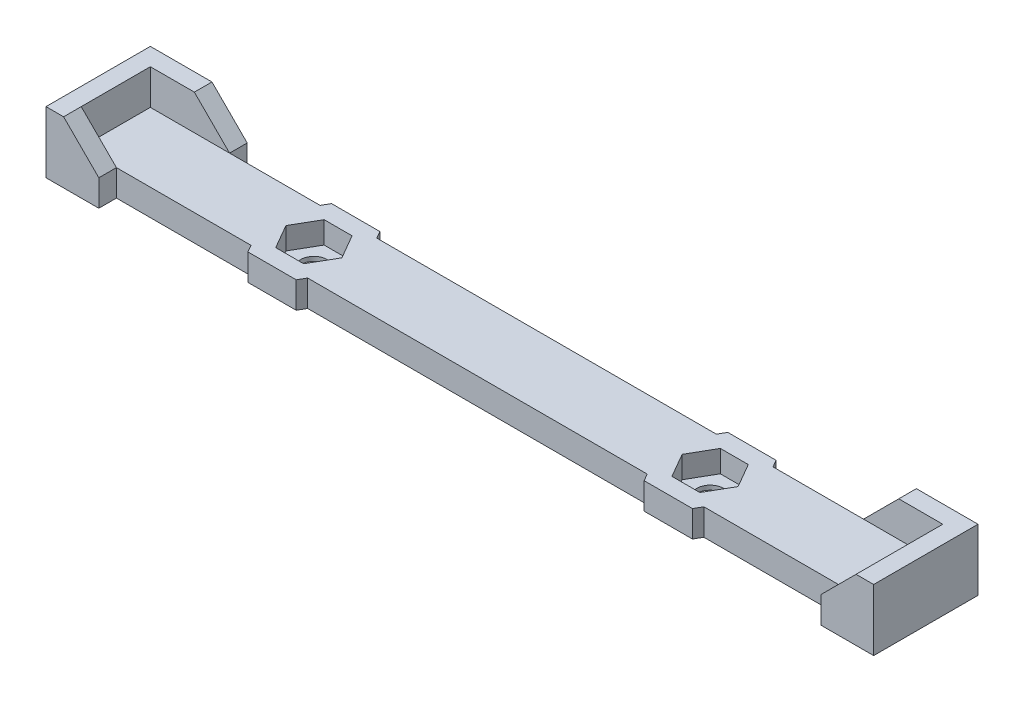
SolidWorks part; units mm, degrees
ref_plane "前视基准面" through (0, 0, 0) normal (0, 0, 1) x (1, 0, 0)
ref_plane "上视基准面" through (0, 0, 0) normal (0, 1, 0) x (1, 0, 0)
ref_plane "右视基准面" through (0, 0, 0) normal (1, 0, 0) x (0, 0, -1)
sketch "草图1" plane through (0, 0, 0) normal (0, 1, 0) x (1, 0, 0)
  line L0 (0, 0) -> (90, 0)
  line L1 (0, 0) -> (0, -7.85)
  line L2 (90, 0) -> (90, -7.85)
  line L3 (0, -7.85) -> (90, -7.85)
  point P7 (91.2972, -17.025)
  dimension "D1" = 90
  dimension "D2" = 7.85
extrude "凸台-拉伸1" add sketch "草图1" along normal blind 2
sketch "草图2" plane through (90, 0, 0) normal (1, 0, 0) x (0, 0, -1)
  line L0 (-7.85, 0) -> (-7.85, 6)
  line L1 (-7.85, 0) -> (0, 0)
  line L2 (-7.85, 6) -> (0, 6)
  line L3 (0, 0) -> (0, 6)
  dimension "D1" = 7.85
  dimension "D2" = 6
extrude "凸台-拉伸2" add sketch "草图2" along normal blind 2
sketch "草图3" plane through (0, 0, 0) normal (-1, 0, 0) x (0, 0, 1)
  line L0 (0, 0) -> (0, 6)
  line L1 (0, 0) -> (7.85, 0)
  line L2 (0, 6) -> (7.85, 6)
  line L3 (7.85, 0) -> (7.85, 6)
  dimension "D1" = 7.85
extrude "凸台-拉伸3" add sketch "草图3" along normal blind 2
sketch "草图4" plane through (0, 0, 0) normal (0, 0, -1) x (-1, 0, 0)
  line L0 (2, 0) -> (2, 6)
  line L1 (2, 6) -> (0, 6)
  line L2 (0, 6) -> (-5, 6)
  line L3 (-5, 6) -> (-9, 2)
  line L4 (-90, 2) -> (0, 2) construction
  line L5 (-9, 2) -> (-9, 0)
  line L6 (-92, 0) -> (2, 0) construction
  line L7 (-9, 0) -> (2, 0)
  line L8 (-92, 0) -> (-92, 6)
  line L9 (-92, 6) -> (-90, 6)
  line L10 (-90, 6) -> (-85, 6)
  line L11 (-85, 6) -> (-81, 2)
  line L12 (-81, 2) -> (-81, 0)
  line L13 (-81, 0) -> (-92, 0)
  dimension "D1" = 5
  dimension "D2" = 4
  dimension "D3" = 5
  dimension "D4" = 4
extrude "凸台-拉伸4" add sketch "草图4" along normal blind 2
sketch "草图5" plane through (0, 0, 7.85) normal (0, 0, 1) x (1, 0, 0)
  line L0 (92, 0) -> (92, 6)
  line L1 (92, 6) -> (90, 6)
  line L2 (90, 6) -> (86, 2)
  line L3 (90, 2) -> (81, 2) construction
  line L4 (86, 2) -> (86, 0)
  line L5 (-2, 0) -> (92, 0) construction
  line L6 (86, 0) -> (92, 0)
  line L7 (-2, 0) -> (-2, 6)
  line L8 (-2, 6) -> (0, 6)
  line L9 (0, 6) -> (4, 2)
  line L10 (9, 2) -> (0, 2) construction
  line L11 (4, 2) -> (4, 0)
  line L12 (4, 0) -> (-2, 0)
  dimension "D1" = 4
  dimension "D2" = 4
extrude "凸台-拉伸5" add sketch "草图5" along normal blind 2
sketch "草图10" plane through (0, 0, 0) normal (0, -1, 0) x (1, 0, 0)
  line L0 (-2, -2) -> (-2, 9.85)
  line L1 (-2, 9.85) -> (4, 9.85)
  line L2 (4, 9.85) -> (4, 7.85)
  line L3 (4, 7.85) -> (86, 7.85)
  line L4 (86, 7.85) -> (86, 9.85)
  line L5 (86, 9.85) -> (92, 9.85)
  line L6 (92, 9.85) -> (92, -2)
  line L7 (92, -2) -> (81, -2)
  line L8 (81, -2) -> (81, 0)
  line L9 (81, 0) -> (9, 0)
  line L10 (9, 0) -> (9, -2)
  line L11 (9, -2) -> (-2, -2)
extrude "凸台-拉伸8" add sketch "草图10" along normal blind 1
sketch "草图12" plane through (0, 2, 0) normal (0, 1, 0) x (1, 0, 0)
  line L4 (25.6754, -3.925) -> (24.0877, -1.175)
  line L5 (24.0877, -1.175) -> (20.9123, -1.175)
  line L6 (20.9123, -1.175) -> (19.3246, -3.925)
  line L7 (19.3246, -3.925) -> (20.9123, -6.675)
  line L8 (20.9123, -6.675) -> (24.0877, -6.675)
  line L9 (24.0877, -6.675) -> (25.6754, -3.925)
  line L11 (70.6754, -3.925) -> (69.0877, -1.175)
  line L12 (69.0877, -1.175) -> (65.9123, -1.175)
  line L13 (65.9123, -1.175) -> (64.3246, -3.925)
  line L14 (64.3246, -3.925) -> (65.9123, -6.675)
  line L15 (65.9123, -6.675) -> (69.0877, -6.675)
  line L16 (69.0877, -6.675) -> (70.6754, -3.925)
  circle A0 centre (22.5, -3.925) radius 2.75 construction
  circle A1 centre (67.5, -3.925) radius 2.75 construction
  dimension "D2" = 5.5
  dimension "D3" = 5.5
extrude "切除-拉伸1" cut sketch "草图12" against normal blind 2.5
sketch "草图13" plane through (0, 2, 0) normal (0, 1, 0) x (1, 0, 0)
  line L1 (27.9848, -3.925) -> (25.2424, 0.825)
  line L2 (25.2424, 0.825) -> (19.7576, 0.825)
  line L3 (19.7576, 0.825) -> (17.0152, -3.925)
  line L4 (17.0152, -3.925) -> (19.7576, -8.675)
  line L5 (19.7576, -8.675) -> (25.2424, -8.675)
  line L6 (24.0877, -6.675) -> (25.6754, -3.925)
  line L7 (25.6754, -3.925) -> (24.0877, -1.175)
  line L8 (24.0877, -1.175) -> (20.9123, -1.175)
  line L9 (20.9123, -1.175) -> (19.3246, -3.925)
  line L10 (19.3246, -3.925) -> (20.9123, -6.675)
  line L11 (20.9123, -6.675) -> (24.0877, -6.675)
  line L12 (24.0877, -6.675) -> (25.6754, -3.925)
  line L13 (25.6754, -3.925) -> (24.0877, -1.175)
  line L14 (24.0877, -1.175) -> (20.9123, -1.175)
  line L15 (20.9123, -1.175) -> (19.3246, -3.925)
  line L16 (19.3246, -3.925) -> (20.9123, -6.675)
  line L17 (20.9123, -6.675) -> (24.0877, -6.675)
  line L18 (69.0877, -6.675) -> (70.6754, -3.925)
  line L19 (70.6754, -3.925) -> (69.0877, -1.175)
  line L20 (69.0877, -1.175) -> (65.9123, -1.175)
  line L21 (65.9123, -1.175) -> (64.3246, -3.925)
  line L22 (64.3246, -3.925) -> (65.9123, -6.675)
  line L23 (65.9123, -6.675) -> (69.0877, -6.675)
  line L24 (69.0877, -6.675) -> (70.6754, -3.925)
  line L25 (70.6754, -3.925) -> (69.0877, -1.175)
  line L26 (69.0877, -1.175) -> (65.9123, -1.175)
  line L27 (65.9123, -1.175) -> (64.3246, -3.925)
  line L28 (64.3246, -3.925) -> (65.9123, -6.675)
  line L29 (65.9123, -6.675) -> (69.0877, -6.675)
  line L30 (25.2424, -8.675) -> (27.9848, -3.925)
  line L31 (72.9848, -3.925) -> (70.2424, 0.825)
  line L32 (70.2424, 0.825) -> (64.7576, 0.825)
  line L33 (64.7576, 0.825) -> (62.0152, -3.925)
  line L34 (62.0152, -3.925) -> (64.7576, -8.675)
  line L35 (64.7576, -8.675) -> (70.2424, -8.675)
  line L36 (70.2424, -8.675) -> (72.9848, -3.925)
  circle A0 centre (22.5, -3.925) radius 4.75 construction
  circle A1 centre (67.5, -3.925) radius 4.75 construction
  dimension "D3" = 2
  dimension "D4" = 2
  dimension "D1" = 0
  dimension "D2" = 0
extrude "凸台-拉伸9" add sketch "草图13" against normal blind 3
sketch "草图15" plane through (0, -0.5, 0) normal (0, 1, 0) x (1, 0, 0)
  circle A0 centre (22.5, -3.925) radius 1.5
  dimension "D1" = 3
extrude "切除-拉伸2" cut sketch "草图15" against normal blind 3
sketch "草图16" plane through (0, -0.5, 0) normal (0, 1, 0) x (1, 0, 0)
  circle A0 centre (67.5, -3.925) radius 1.5
  dimension "D1" = 3
extrude "切除-拉伸3" cut sketch "草图16" against normal blind 3
